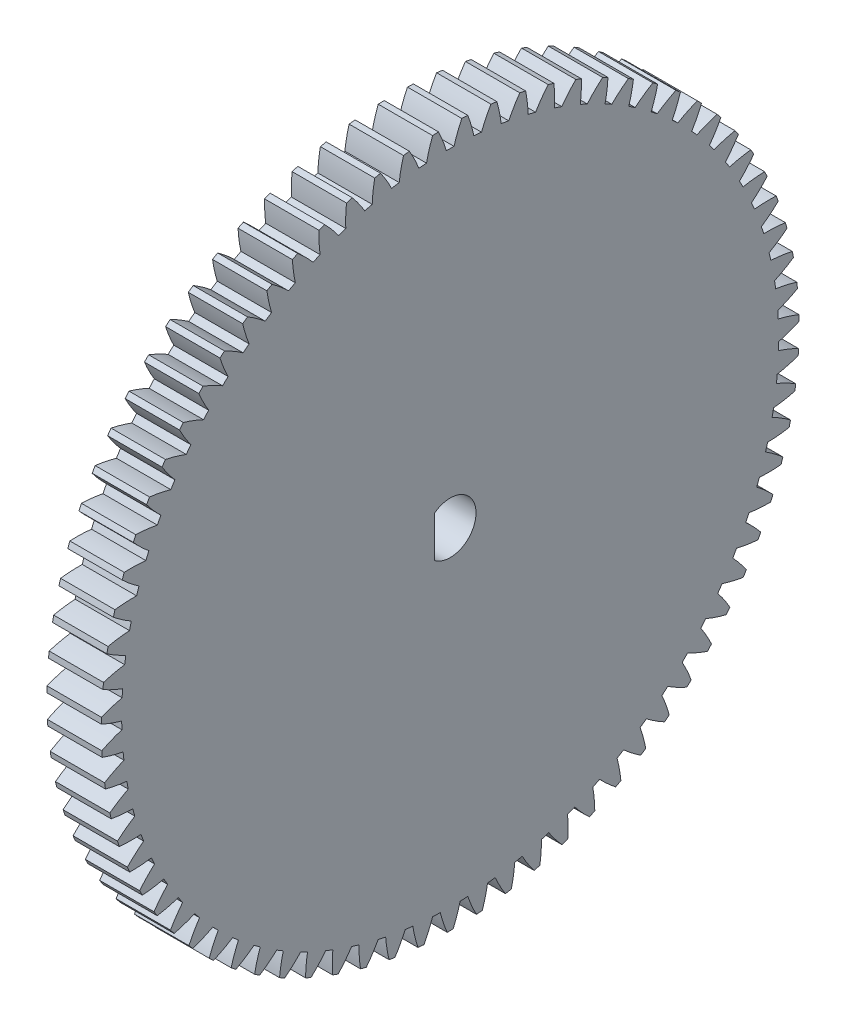
SolidWorks part; units mm, degrees
ref_plane "Plane1" through (0, 0, 0) normal (0, 0, 1) x (1, 0, 0)
ref_plane "Plane2" through (0, 0, 0) normal (0, 1, 0) x (1, 0, 0)
ref_plane "Plane3" through (0, 0, 0) normal (1, 0, 0) x (0, 0, -1)
sketch "HoldingSke" plane through (0, 0, 0) normal (0, 1, 0) x (1, 0, 0)
  line L0 (0, 0) -> (0.2588, -0.9659)
  line L1 (-15, 0) -> (100, 0) construction
  line L2 (0, 0) -> (-2.1039, 2.3779)
  line L3 (0, 0) -> (-11.863, 4.5341)
  line L4 (0, 0) -> (2.2352, 8.3417)
  line L5 (0, 0) -> (-46.8476, -17.4728)
  line L6 (0, 0) -> (-4.9738, -3.3558)
  line L7 (-2.1039, 2.3779) -> (8.6587, 51.2063)
  line L8 (-76.2, 54.61) -> (-75.2, 54.61)
  line L9 (-71.009, 38.7566) -> (-53.1078, 45.2721)
  line L10 (-76.2, 71.12) -> (104.1128, 71.12)
  line L11 (0, 0) -> (-6, 0)
  line L12 (-76.2, 101.6) -> (-76.162, 101.6)
  line L13 (24.9733, 27.94) -> (52.9518, 28.4284)
  line L14 (24.9733, 27.94) -> (24.9743, 27.94)
  line L15 (24.9733, 27.94) -> (100.4006, 29.5858)
  line L16 (-63.627, -1) -> (-12.827, -1)
  circle A0 centre (0, 0) radius 3
  circle A1 centre (0, 0) radius 36.249
  circle A2 centre (0, 0) radius 37.5
  circle A3 centre (0, 0) radius 3
  dimension "MHD" = 72.498
  dimension "Hub_dia" = 75
  dimension "Bore" = 6
  dimension "MBD" = 6
  dimension "Num_teeth" = 75
  dimension "Pitch" = 1
  dimension "Overall_len" = 50
  dimension "Show_teeth" = 75
  dimension "Thickness" = 6
  dimension "OAL" = 50.0005
  dimension "T_dim" = 1
  dimension "Ap" = 20
  dimension "H" = 19.05
  dimension "Pitch_radius" = 180.3128
  dimension "Width" = 6
  dimension "Backlash" = 0.038
  dimension "Addendum_fac" = 1
  dimension "Dedendum_fac" = 1.25
  dimension "Clearance_fac" = 0.25
  dimension "Dedendum_add" = 0.001
  dimension "Module" = 1
sketch "BasProSke" plane through (0, 0, 0) normal (0, 1, 0) x (1, 0, 0)
  line L0 (-10, 0) -> (60, 0) construction
  line L1 (0, 0) -> (0, 38.5)
  line L2 (0, 0) -> (6, 0)
  line L3 (6, 0) -> (6, 38.5)
  line L4 (6, 38.5) -> (0, 38.5)
  dimension "Thickness" = 6
  dimension "Diameter" = 77
revolve "Base-Revolve" add sketch "BasProSke" angle 360 about L0
sketch "TooCutSke" plane through (0, 0, 0) normal (1, 0, 0) x (0, 0, -1)
  line L1 (0, 0) -> (0, 107) construction
  line L2 (0, 0) -> (-0.8518, 37.4903) construction
  line L3 (0, 0) -> (-3.1401, 74.9204) construction
  line L4 (-0.8518, 37.4903) -> (-1.57, 37.4602) construction
  arc A0 (0.4225, 36.2465) -> (-0.4225, 36.2465) centre (0, 0) ccw
  arc A1 (1.296, 38.5036) -> (-1.296, 38.5036) centre (0, 0) ccw
  circle A2 centre (0, 0) radius 37.5 construction
  circle A3 centre (0, 0) radius 35.2385 construction
  arc A4 (-0.4225, 36.2465) -> (-1.296, 38.5036) centre (-14.8025, 31.9787) ccw
  arc A5 (1.296, 38.5036) -> (0.4225, 36.2465) centre (14.8025, 31.9787) ccw
  dimension "Root_dia" = 72.498
  dimension "Overcut_dia" = 77.0508
  dimension "Pitch_dia" = 75
  dimension "Base_dia" = 70.4769
  dimension "Flank_rad" = 15
  dimension "Half_ang" = 2.4
  dimension "Half_CT" = 0.7188
extrude "ToothCut" cut sketch "TooCutSke" along normal through all
fillet "Breaks" [suppressed] radius 0.02
fillet "RootFillets" [suppressed] radius 0.251
pattern_circular "TeethCuts" count 75 every 4.8 about axis through (-10, 0, 0) along (1, 0, 0) of "ToothCut", "RootFillets", "Breaks"
sketch "HubNeaOneSke" plane through (0, 0, 0) normal (-1, 0, 0) x (0, 0, 1)
  circle A0 centre (0, 0) radius 36.249
  dimension "Diameter" = 72.498
extrude "HubNearOne" [suppressed] add sketch "HubNeaOneSke" along normal blind 44.0005
sketch "HubNeaBotSke" plane through (0, 0, 0) normal (-1, 0, 0) x (0, 0, 1)
  circle A0 centre (0, 0) radius 36.249
  dimension "Diameter" = 72.498
extrude "HubNearBoth" [suppressed] add sketch "HubNeaBotSke" along normal blind 22.0003
ref_plane "FarPln" through (6, 0, 0) normal (1, 0, 0) x (0, 0, -1)
sketch "HubFarSke" plane through (6, 0, 0) normal (1, 0, 0) x (0, 0, -1)
  circle A0 centre (0, 0) radius 36.249
  dimension "Diameter" = 72.498
extrude "HubFar" [suppressed] add sketch "HubFarSke" along normal blind 22.0003
sketch "KeySke" plane through (0, 0, 0) normal (1, 0, 0) x (0, 0, -1)
  line L0 (-1, 0) -> (-1, 4)
  line L1 (-1, 4) -> (1, 4)
  line L2 (1, 4) -> (1, 0)
  line L3 (0, 0) -> (0, 34) construction
  line L4 (-1, 0) -> (1, 0)
  dimension "Offset" = 4
  dimension "Width" = 2
extrude "Keyway" [suppressed] cut sketch "KeySke" along normal mid plane 100.001
pattern_circular "Keyway2" [suppressed] count 2 every 90 about axis through (-10, 0, 0) along (1, 0, 0)
sketch "Sketch2" plane through (6, 0, 0) normal (1, 0, 0) x (0, 0, -1)
  line L0 (-1.7493, 2.25) -> (-1.7493, -2.25)
  arc A0 (-1.7493, -2.25) -> (-1.7493, 2.25) centre (0, 0) ccw
  dimension "D1" = 5.7
  dimension "D2" = 4.5
extrude "Cut-Extrude3" cut sketch "Sketch2" against normal through all
equation "' \"Module@HoldingSke\" = 6.35"
equation "' \"Num_teeth@HoldingSke\" = 12"
equation "' \"Ap@HoldingSke\" =  20"
equation "' \"Ap@HoldingSke\" = 20"
equation "' \"Width@HoldingSke\" = 0.5 * 25.4"
equation "' \"Hub_dia@HoldingSke\"= 1 * 25.4"
equation "' \"Hub_dia@HoldingSke\" = 1 * 25.4"
equation "' \"Overall_len@HoldingSke\" = 1.0 * 25.4"
equation "' \"Bore@HoldingSke\" = 0.75 * 25.4"
equation "' \"T_dim@HoldingSke\" = 0.1 * 25.4"
equation "' \"Width@KeySke\" = 0.25 * 25.4"
equation "' \"Show_teeth@HoldingSke\" = 13"
equation "' \"Backlash@HoldingSke\" = 0.009 * 25.4"
equation "' \"Addendum_fac@HoldingSke\" = 1.0"
equation "' \"Dedendum_fac@HoldingSke\" = 1.25"
equation "' \"Dedendum_add@HoldingSke\" = 0.00005 * 25.4"
equation "' \"Clearance_fac@HoldingSke\" = 0.25"
equation "\"Pitch@HoldingSke\" = 1 / \"Module@HoldingSke\""
equation "\"Overcut_dia@TooCutSke\" = (\"Num_teeth@HoldingSke\" + 2 * \"Addendum_fac@HoldingSke\") / \"Pitch@HoldingSke\" + 0.002 * 25.4"
equation "\"Pitch_dia@TooCutSke\" = \"Num_teeth@HoldingSke\" / \"Pitch@HoldingSke\""
equation "\"Base_dia@TooCutSke\" = \"Num_teeth@HoldingSke\" / \"Pitch@HoldingSke\" * cos((\"Ap@HoldingSke\"  * 3.14159265 / 180))"
equation "\"Root_dia@TooCutSke\" = (\"Num_teeth@HoldingSke\" + 2) / \"Pitch@HoldingSke\" - 2 * (\"Addendum_fac@HoldingSke\" + \"Dedendum_fac@HoldingSke\") / \"Pitch@HoldingSke\" - \"Dedendum_add@HoldingSke\" * 2"
equation "\"Half_ang@TooCutSke\" = 180 / \"Num_teeth@HoldingSke\""
equation "\"Half_CT@TooCutSke\" = \"Num_teeth@HoldingSke\" / \"Pitch@HoldingSke\" * sin((3.14159265 / 2 / \"Num_teeth@HoldingSke\")) / 2 - 7 * \"Backlash@HoldingSke\" / 4"
equation "\"Flank_rad@TooCutSke\" = \"Num_teeth@HoldingSke\" / \"Pitch@HoldingSke\" / 5"
equation "\"Radius@RootFillets\" = \"Clearance_fac@HoldingSke\" / \"Pitch@HoldingSke\" + \"Dedendum_add@HoldingSke\""
equation "\"Break_rad@Breaks\" = 0.02 / \"Pitch@HoldingSke\""
equation "\"Thickness@HoldingSke\" = \"Width@HoldingSke\""
equation "\"OAL@HoldingSke\" = \"Thickness@HoldingSke\""
equation "\"MHD@HoldingSke\" = (\"Num_teeth@HoldingSke\" + 2) / \"Pitch@HoldingSke\" - 2 * (\"Addendum_fac@HoldingSke\" + \"Dedendum_fac@HoldingSke\")  / \"Pitch@HoldingSke\" - \"Dedendum_add@HoldingSke\" * 2"
equation "\"MBD@HoldingSke\" = (\"Num_teeth@HoldingSke\" + 2) / \"Pitch@HoldingSke\" - 2 * (\"Addendum_fac@HoldingSke\" + \"Dedendum_fac@HoldingSke\")  / \"Pitch@HoldingSke\" - \"Dedendum_add@HoldingSke\" * 2 - 0.002 * 25.4"
equation "\"MHD@HoldingSke\" = ((sgn( \"MHD@HoldingSke\" - \"Hub_dia@HoldingSke\" )-1)*( \"MHD@HoldingSke\" - \"Hub_dia@HoldingSke\" ))/-2+ \"Hub_dia@HoldingSke\""
equation "\"MBD@HoldingSke\" = ((sgn( \"MBD@HoldingSke\" - \"Bore@HoldingSke\" )-1)*( \"MBD@HoldingSke\" - \"Bore@HoldingSke\" ))/-2+ \"Bore@HoldingSke\""
equation "\"OAL@HoldingSke\" = ((sgn( \"OAL@HoldingSke\" - \"Overall_len@HoldingSke\" )+1)*( \"OAL@HoldingSke\" - \"Overall_len@HoldingSke\" ))/2 + \"Overall_len@HoldingSke\" + 0.000002 * 25.4"
equation "\"Num_teeth@TeethCuts\" = int( \"Show_teeth@HoldingSke\" ) + 1"
equation "\"Num_teeth@TeethCuts\" = ((sgn( \"Num_teeth@TeethCuts\" - \"Num_teeth@HoldingSke\" )-1)*( \"Num_teeth@TeethCuts\" - \"Num_teeth@HoldingSke\" ))/-2+ \"Num_teeth@HoldingSke\""
equation "\"Num_teeth@TeethCuts\" = ((sgn( \"Num_teeth@TeethCuts\" - 2.0)+1)*( \"Num_teeth@TeethCuts\" - 2.0))/2 +2.0"
equation "\"Angle@TeethCuts\" = 360.0 / \"Num_teeth@HoldingSke\""
equation "\"Diameter@BasProSke\" = (\"Num_teeth@HoldingSke\" + 2 * \"Addendum_fac@HoldingSke\") / \"Pitch@HoldingSke\""
equation "\"Thickness@BasProSke\"  = \"Thickness@HoldingSke\""
equation "' \"Fillet_rad@BasProSke\" =  \"Thickness@HoldingSke\" * 0.05"
equation "' \"Fillet_rad@BasProSke\" = \"Thickness@HoldingSke\" * 0.05"
equation "\"MHD@HoldingSke\" = ((sgn( \"MHD@HoldingSke\" - \"Root_dia@TooCutSke\" )-1)*( \"MHD@HoldingSke\" - \"Root_dia@TooCutSke\" ))/-2+ \"Root_dia@TooCutSke\""
equation "\"Diameter@HubNeaOneSke\" = \"MHD@HoldingSke\""
equation "\"Length@HubNearOne\" = \"OAL@HoldingSke\" - \"Thickness@BasProSke\""
equation "\"Diameter@HubNeaBotSke\" = \"MHD@HoldingSke\""
equation "\"Length@HubNearBoth\" = ( \"OAL@HoldingSke\" - \"Thickness@BasProSke\" ) / 2.0"
equation "\"Thickness@FarPln\" = \"Thickness@BasProSke\""
equation "\"Diameter@HubFarSke\" = \"MHD@HoldingSke\""
equation "\"Length@HubFar\" = ( \"OAL@HoldingSke\" - \"Thickness@BasProSke\" ) / 2.0"
equation "\"D1@Keyway\" = \"OAL@HoldingSke\" * 2.0"
equation "\"Offset@KeySke\" = \"T_dim@HoldingSke\" + \"MBD@HoldingSke\" / 2.0"
